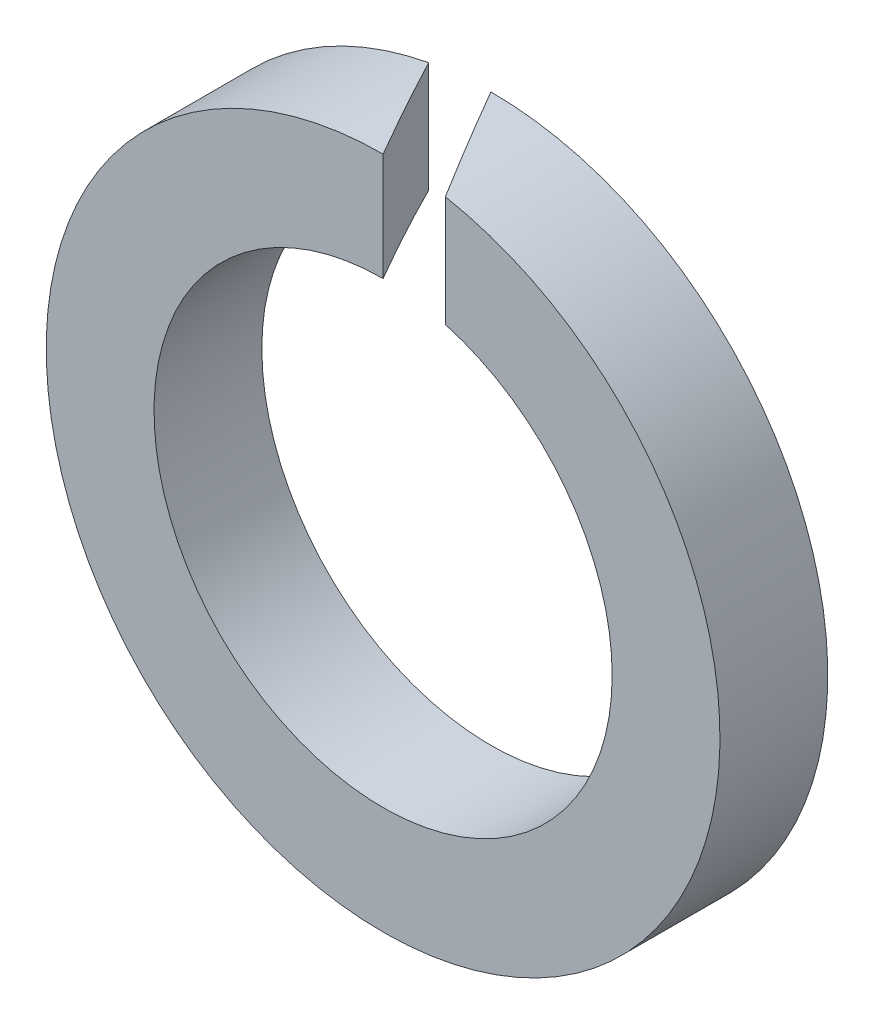
SolidWorks part; units mm, degrees
ref_plane "Front" through (0, 0, 0) normal (0, 0, 1) x (1, 0, 0)
ref_plane "Top" through (0, 0, 0) normal (0, 1, 0) x (1, 0, 0)
ref_plane "Right" through (0, 0, 0) normal (1, 0, 0) x (0, 0, -1)
sketch "Sketch1" plane through (0, 0, 0) normal (0, 0, 1) x (1, 0, 0)
  circle A0 centre (0, 0) radius 1.7
  circle A1 centre (0, 0) radius 2.5
  dimension "d" = 3.4
  dimension "b" = 0.8
extrude "Base-Extrude" add sketch "Sketch1" against normal blind 0.8
sketch "Sketch2" plane through (0, 0, 0) normal (0, 1, 0) x (1, 0, 0)
  line L0 (0, 0.8) -> (0.4619, 0)
  line L1 (0.4619, 0) -> (0, 0)
  line L3 (0, 0) -> (-0.4619, 0.8)
  line L5 (-0.4619, 0.8) -> (0, 0.8)
  line L7 (2.5, 0.8) -> (-2.5, 0.8) construction
  dimension "m" = 0.4
extrude "Cut-Extrude1" cut sketch "Sketch2" along normal through all
